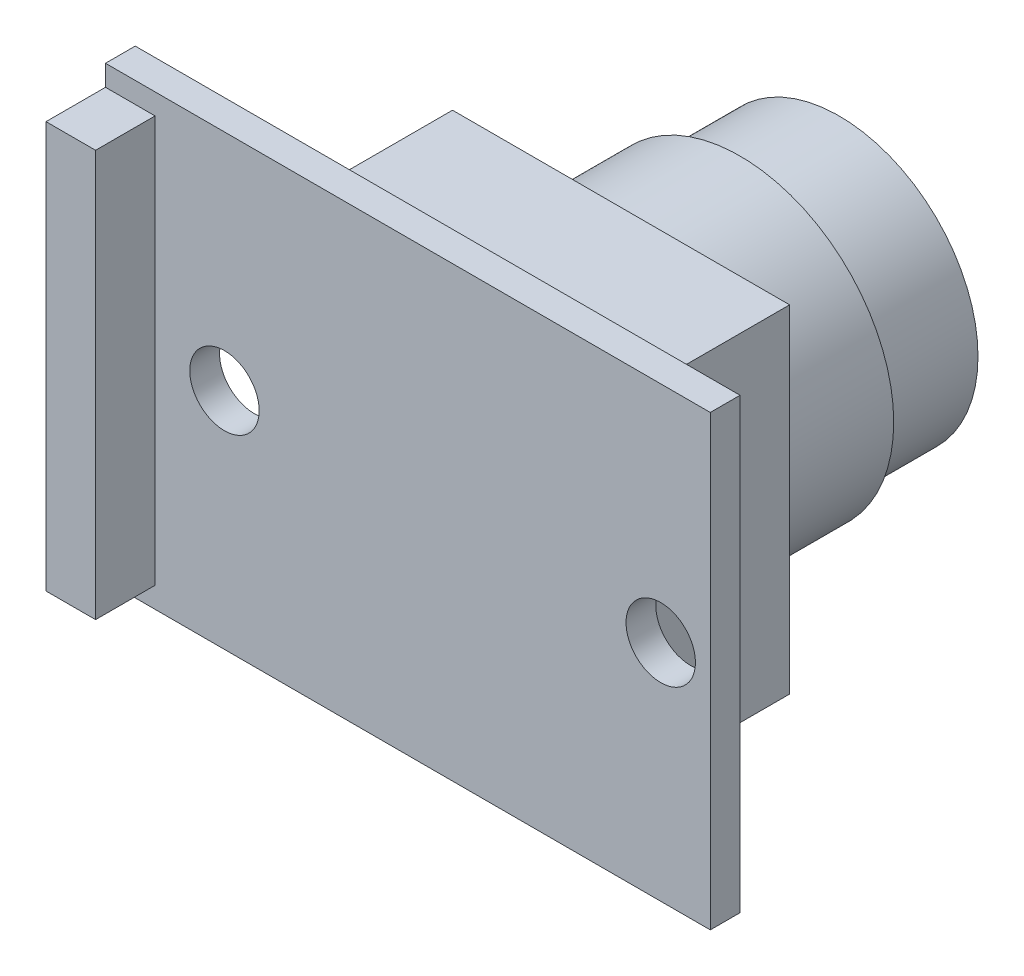
SolidWorks part; units mm, degrees
ref_plane "前视基准面" through (0, 0, 0) normal (0, 0, 1) x (1, 0, 0)
ref_plane "上视基准面" through (0, 0, 0) normal (0, 1, 0) x (1, 0, 0)
ref_plane "右视基准面" through (0, 0, 0) normal (1, 0, 0) x (0, 0, -1)
sketch "草图1" plane through (0, 0, 0) normal (0, 0, 1) x (1, 0, 0)
  circle A0 centre (0, 0) radius 7
  dimension "D1" = 14
extrude "凸台-拉伸1" add sketch "草图1" along normal blind 5
sketch "草图2" plane through (0, 0, 5) normal (0, 0, 1) x (1, 0, 0)
  circle A0 centre (0, 0) radius 7.75
  dimension "D1" = 15.5
extrude "凸台-拉伸2" add sketch "草图2" along normal blind 6
sketch "草图3" plane through (0, 0, 11) normal (0, 0, 1) x (1, 0, 0)
  line L1 (-8.5, 8.5) -> (8.5, 8.5)
  line L2 (-8.5, 8.5) -> (-8.5, -8.5)
  line L3 (-8.5, -8.5) -> (8.5, -8.5)
  line L4 (8.5, 8.5) -> (8.5, -8.5)
  point P4 (0, 8.5)
  point P6 (-8.5, 0)
  dimension "D1" = 17
  dimension "D2" = 17
extrude "凸台-拉伸3" add sketch "草图3" along normal blind 8
sketch "草图4" plane through (0, 0, 19) normal (0, 0, 1) x (1, 0, 0)
  line L0 (8.5, -8.5) -> (8.5, 8.5) construction
  line L1 (-16.5, 11.3) -> (14, 11.3)
  line L2 (-16.5, 11.3) -> (-16.5, -11.3)
  line L3 (-16.5, -11.3) -> (14, -11.3)
  line L4 (14, 11.3) -> (14, -11.3)
  line L5 (-8.5, 8.5) -> (-8.5, -8.5) construction
  line L6 (8.5, 8.5) -> (-8.5, 8.5) construction
  line L7 (-8.5, -8.5) -> (8.5, -8.5) construction
  circle A0 centre (11.5, 0) radius 1.75
  circle A1 centre (-10.5, 0) radius 1.75
  point P16 (0, 0)
  dimension "D7" = 3.5
  dimension "D8" = 3.5
  dimension "D1" = 5.5
  dimension "D2" = 8
  dimension "D3" = 2.8
  dimension "D4" = 2.8
  dimension "D5" = 3
  dimension "D6" = 22
extrude "凸台-拉伸4" add sketch "草图4" along normal blind 1.5
sketch "草图5" plane through (0, 0, 20.5) normal (0, 0, 1) x (1, 0, 0)
  line L0 (-16.5, 11.3) -> (-16.5, -11.3) construction
  line L1 (-16.5, 10.25) -> (-14, 10.25)
  line L2 (-16.5, 10.25) -> (-16.5, -10.25)
  line L3 (-16.5, -10.25) -> (-14, -10.25)
  line L4 (-14, 10.25) -> (-14, -10.25)
  line L5 (14, -11.3) -> (14, 11.3) construction
  point P8 (14, 0)
  point P9 (-14, 0)
  dimension "D1" = 20.5
  dimension "D2" = 2.5
extrude "凸台-拉伸5" add sketch "草图5" along normal blind 3
